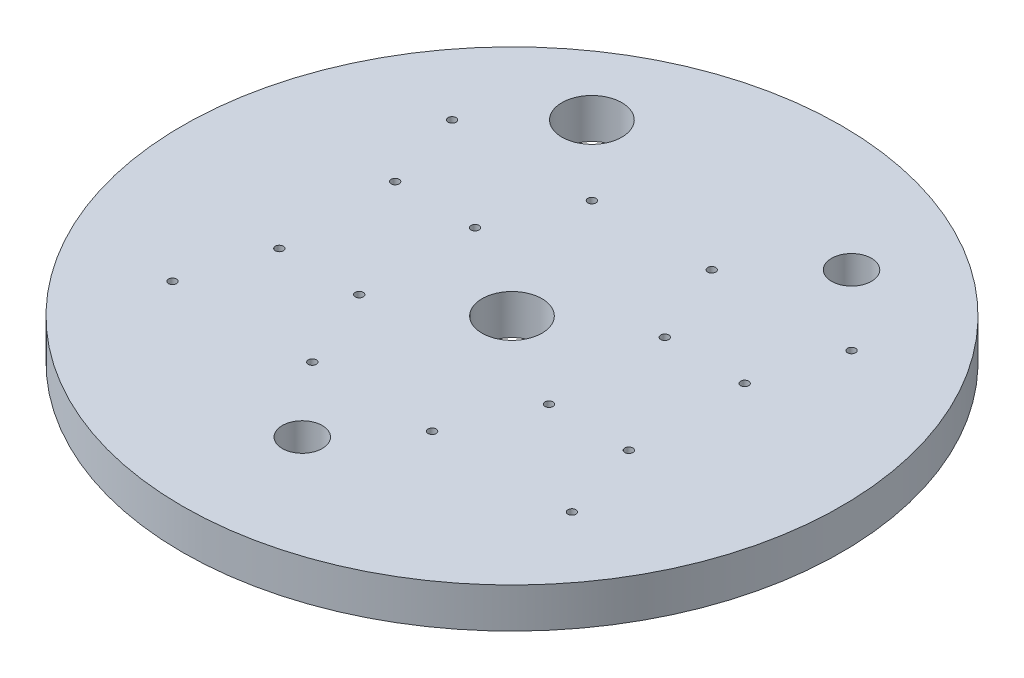
SolidWorks part; units mm, degrees
material "6061 Alloy"
ref_plane "Front Plane" through (0, 0, 0) normal (0, 0, 1) x (1, 0, 0)
ref_plane "Top Plane" through (0, 0, 0) normal (0, 1, 0) x (1, 0, 0)
ref_plane "Right Plane" through (0, 0, 0) normal (1, 0, 0) x (0, 0, -1)
sketch "Sketch1" plane through (0, 0, 0) normal (0, 1, 0) x (1, 0, 0)
  circle A0 centre (0, 0) radius 209.55
extrude "Boss-Extrude1" add sketch "Sketch1" along normal mid plane 25.4
hole_wizard "3/8-16 Tapped Hole1" positions "Sketch3" profile "Sketch2" tap size "3/8-16" standard "ANSI Inch"
sketch "Sketch3" plane through (0, -12.7, 0) normal (0, -1, 0) x (-1, 0, 0)
  point P0 (88.9, -88.9)
  point P2 (-88.9, -88.9)
  point P4 (-88.9, 88.9)
  point P6 (88.9, 88.9)
  dimension "D1" = 88.9
  dimension "D2" = 88.9
  dimension "D3" = 88.9
  dimension "D4" = 88.9
sketch "Sketch2" plane through (-88.9, -12.7, 88.9) normal (1, 0, 0) x (0, 0, -1)
  line L0 (0, 0) -> (0, 21.6887)
  line L1 (0, 21.6887) -> (3.9687, 19.304)
  line L2 (3.9687, 19.304) -> (3.9687, 0)
  line L5 (3.9687, 0) -> (0, 0)
  line L10 (0, 21.6887) -> (-3.9688, 19.304) construction
  line L11 (0, -6.35) -> (0, 107.95) construction
  dimension "Tap Drill Dia." = 7.9375
  dimension "Tap Drill Depth" = 19.304
  dimension "Drill Angle" = 118
cosmetic thread "Hole Thread1" parameters "D1"=13.97, "D2"=9.525
cosmetic thread "Hole Thread2" parameters "D1"=13.97, "D2"=9.525
cosmetic thread "Hole Thread3" parameters "D1"=13.97, "D2"=9.525
cosmetic thread "Hole Thread4" parameters "D1"=13.97, "D2"=9.525
sketch "Sketch4" plane through (0, 12.7, 0) normal (0, 1, 0) x (1, 0, 0)
  circle A0 centre (0, 0) radius 19.05
extrude "Cut-Extrude1" cut sketch "Sketch4" against normal up to next
sketch "Sketch5" plane through (0, 12.7, 0) normal (0, 1, 0) x (1, 0, 0)
  circle A0 centre (0, -133.35) radius 12.7
  circle A1 centre (82.55, 133.35) radius 12.7
  dimension "D1" = 133.35
  dimension "D2" = 82.55
  dimension "D3" = 133.35
extrude "Cut-Extrude2" cut sketch "Sketch5" against normal up to next
sketch "Sketch6" plane through (0, 12.7, 0) normal (0, 1, 0) x (1, 0, 0)
  circle A0 centre (-82.55, 133.35) radius 19.05
  dimension "D1" = 133.35
  dimension "D2" = 82.55
extrude "Cut-Extrude3" cut sketch "Sketch6" against normal up to next
hole_wizard "1/4-20 Tapped Hole1" positions "Sketch8" profile "Sketch7" tap size "1/4-20" standard "ANSI Inch"
sketch "Sketch8" plane through (0, 12.7, 0) normal (0, 1, 0) x (1, 0, 0)
  point P0 (-111.125, 36.83)
  point P2 (-60.325, 36.83)
  dimension "D1" = 36.83
  dimension "D2" = 50.8
  dimension "D3" = 60.325
sketch "Sketch7" plane through (-111.125, 12.7, -36.83) normal (1, 0, 0) x (0, 0, 1)
  line L0 (0, 0) -> (0, 20.5838)
  line L1 (0, 20.5838) -> (2.5527, 19.05)
  line L2 (2.5527, 19.05) -> (2.5527, 0)
  line L5 (2.5527, 0) -> (0, 0)
  line L10 (0, 20.5838) -> (-2.5527, 19.05) construction
  line L11 (0, -6.35) -> (0, 107.95) construction
  dimension "Tap Drill Dia." = 5.1054
  dimension "Tap Drill Depth" = 19.05
  dimension "Drill Angle" = 118
cosmetic thread "Hole Thread5" parameters "D1"=12.7, "D2"=6.35
cosmetic thread "Hole Thread6" parameters "D1"=12.7, "D2"=6.35
hole_wizard "1/4-20 Tapped Hole2" positions "Sketch10" profile "Sketch9" tap size "1/4-20" standard "ANSI Inch"
sketch "Sketch10" plane through (0, 12.7, 0) normal (0, 1, 0) x (1, 0, 0)
  point P0 (-38.1, 88.9)
  point P2 (-127, 88.9)
  dimension "D1" = 88.9
  dimension "D2" = 38.1
  dimension "D3" = 88.9
sketch "Sketch9" plane through (-38.1, 12.7, -88.9) normal (1, 0, 0) x (0, 0, 1)
  line L0 (0, 0) -> (0, 20.5838)
  line L1 (0, 20.5838) -> (2.5527, 19.05)
  line L2 (2.5527, 19.05) -> (2.5527, 0)
  line L5 (2.5527, 0) -> (0, 0)
  line L10 (0, 20.5838) -> (-2.5527, 19.05) construction
  line L11 (0, -6.35) -> (0, 107.95) construction
  dimension "Tap Drill Dia." = 5.1054
  dimension "Tap Drill Depth" = 19.05
  dimension "Drill Angle" = 118
cosmetic thread "Hole Thread7" parameters "D1"=12.7, "D2"=6.35
cosmetic thread "Hole Thread8" parameters "D1"=12.7, "D2"=6.35
mirror "Mirror1" about plane through (0, 0, 0) normal (1, 0, 0) of "1/4-20 Tapped Hole2", "1/4-20 Tapped Hole1"
mirror "Mirror2" about plane through (0, 0, 0) normal (0, 0, 1) of "Mirror1", "1/4-20 Tapped Hole2", "1/4-20 Tapped Hole1"
sketch "Sketch11" plane through (0, 12.7, 0) normal (0, 1, 0) x (1, 0, 0)
  circle A0 centre (0, 0) radius 195.58
  circle A1 centre (0, 0) radius 191.77
hole_wizard "1/4-20 Tapped Hole3" positions "Sketch13" profile "Sketch12" tap size "1/4-20" standard "ANSI Inch"
sketch "Sketch13" plane through (0, -12.7, 0) normal (0, -1, 0) x (-1, 0, 0)
  point P0 (177.8, -25.4)
  point P2 (127, -25.4)
  point P4 (127, 25.4)
  point P6 (177.8, 25.4)
  dimension "D1" = 50.8
  dimension "D2" = 127
  dimension "D3" = 25.4
  dimension "D4" = 25.4
sketch "Sketch12" plane through (-177.8, -12.7, 25.4) normal (1, 0, 0) x (0, 0, -1)
  line L0 (0, 0) -> (0, 20.5838)
  line L1 (0, 20.5838) -> (2.5527, 19.05)
  line L2 (2.5527, 19.05) -> (2.5527, 0)
  line L5 (2.5527, 0) -> (0, 0)
  line L10 (0, 20.5838) -> (-2.5527, 19.05) construction
  line L11 (0, -6.35) -> (0, 107.95) construction
  dimension "Tap Drill Dia." = 5.1054
  dimension "Tap Drill Depth" = 19.05
  dimension "Drill Angle" = 118
cosmetic thread "Hole Thread9" parameters "D1"=12.7, "D2"=6.35
cosmetic thread "Hole Thread10" parameters "D1"=12.7, "D2"=6.35
cosmetic thread "Hole Thread11" parameters "D1"=12.7, "D2"=6.35
cosmetic thread "Hole Thread12" parameters "D1"=12.7, "D2"=6.35
mirror "Mirror3" about plane through (0, 0, 0) normal (1, 0, 0) of "1/4-20 Tapped Hole3"
